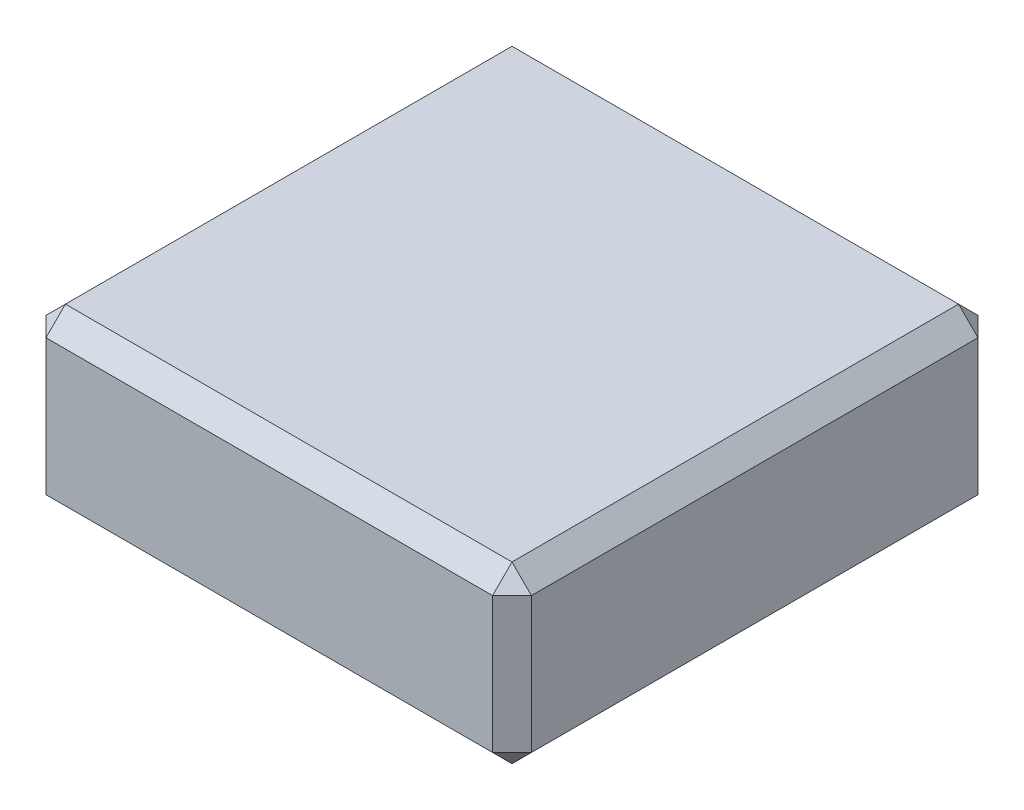
SolidWorks part; units mm, degrees
material "Acrylic (Medium-high impact)"
ref_plane "Front Plane" through (0, 0, 0) normal (0, 0, 1) x (1, 0, 0)
ref_plane "Top Plane" through (0, 0, 0) normal (0, 1, 0) x (1, 0, 0)
ref_plane "Right Plane" through (0, 0, 0) normal (1, 0, 0) x (0, 0, -1)
sketch "Sketch1" plane through (0, 0, 0) normal (0, 1, 0) x (1, 0, 0)
  line L0 (0, 0) -> (50, 0)
  line L1 (0, 0) -> (0, -50)
  line L2 (50, 0) -> (50, -50)
  line L3 (0, -50) -> (50, -50)
  dimension "D1" = 50
  dimension "D2" = 50
extrude "Boss-Extrude1" add sketch "Sketch1" along normal blind 18
chamfer "Chamfer1" distance 2 angle 45 12 edges at (25, 18, 0) (25, 0, 0) (25, 18, 50) (0, 9, 0) (0, 18, 25) (0, 9, 50) (0, 0, 25) (25, 0, 50) (50, 9, 50) (50, 18, 25) (50, 9, 0) (50, 0, 25)
